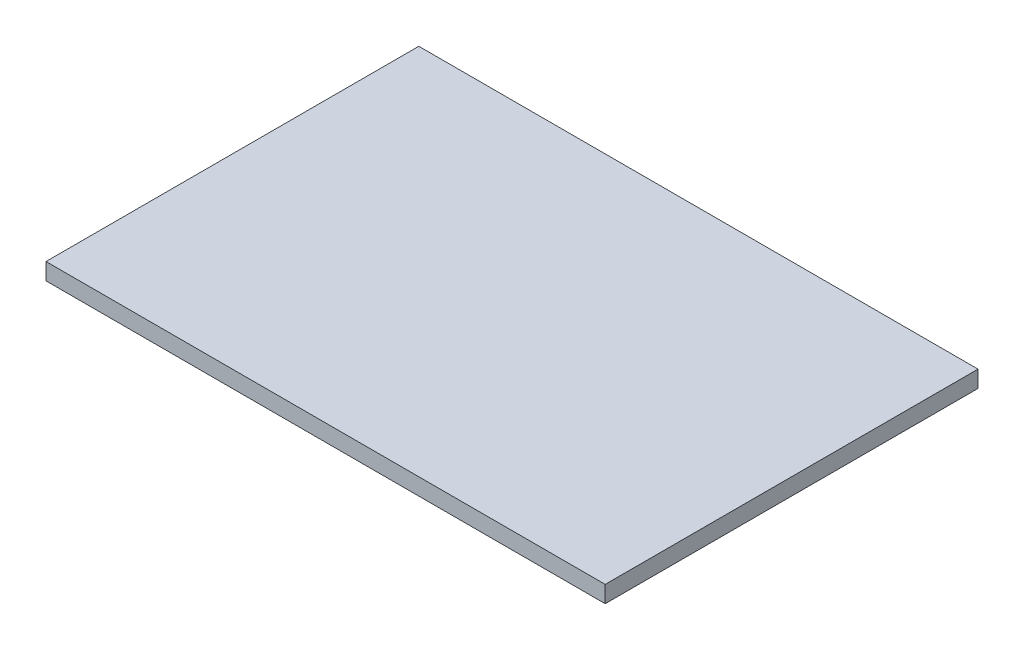
SolidWorks part; units mm, degrees
ref_plane "前视基准面" through (0, 0, 0) normal (0, 0, 1) x (1, 0, 0)
ref_plane "上视基准面" through (0, 0, 0) normal (0, 1, 0) x (1, 0, 0)
ref_plane "右视基准面" through (0, 0, 0) normal (1, 0, 0) x (0, 0, -1)
other "Configuration Table"
sketch "草图1" plane through (0, 0, 0) normal (0, 1, 0) x (1, 0, 0)
  line L1 (-150, 100) -> (150, 100)
  line L2 (-150, 100) -> (-150, -100)
  line L3 (-150, -100) -> (150, -100)
  line L4 (150, 100) -> (150, -100)
  line L5 (-150, 100) -> (150, -100) construction
  line L6 (-150, -100) -> (150, 100) construction
  point P0 (0, 0)
  dimension "D1" = 300
  dimension "D2" = 200
extrude "凸台-拉伸1" add sketch "草图1" along normal blind 9
